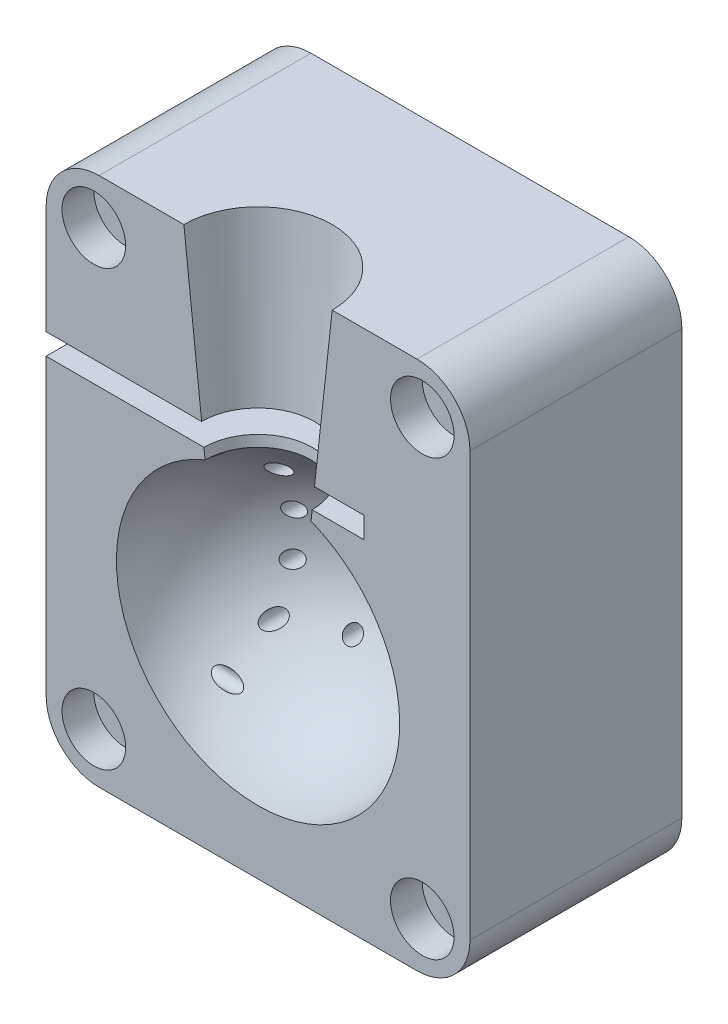
SolidWorks part; units mm, degrees
ref_plane "Alzado" through (0, 0, 0) normal (0, 0, 1) x (1, 0, 0)
ref_plane "Planta" through (0, 0, 0) normal (0, 1, 0) x (1, 0, 0)
ref_plane "Vista lateral" through (0, 0, 0) normal (1, 0, 0) x (0, 0, -1)
sketch "Sketch1" plane through (0, 0, 0) normal (0, 0, 1) x (1, 0, 0)
  line L0 (0, 0) -> (0, 50)
  line L1 (0, 50) -> (-40, 50)
  line L2 (-40, 50) -> (-40, 0)
  line L3 (-40, 0) -> (0, 0)
  dimension "D1" = 40
  dimension "D2" = 50
extrude "Boss-Extrude1" add sketch "Sketch1" against normal blind 20
sketch "Sketch2" plane through (0, 0, 0) normal (0, 0, 1) x (1, 0, 0)
  line L0 (-40, 50) -> (0, 50) construction
  line L1 (-20, 50) -> (-20, 0) construction
  line L2 (-40, 0) -> (0, 0) construction
  line L3 (-20, 32.73) -> (-20, 6)
  arc A0 (-20, 32.73) -> (-20, 6) centre (-20, 19.365) ccw
  dimension "D1" = 26.73
  dimension "D2" = 6
revolve "Cut-Revolve4" cut sketch "Sketch2" angle 360 about L1
sketch "Sketch3" plane through (0, 0, 0) normal (0, 0, 1) x (1, 0, 0)
  line L0 (-40, 50) -> (0, 50) construction
  line L1 (-20, -8.8718) -> (-20, 57.4274) construction
  line L2 (-27, 50) -> (-25, 31.7595)
  line L3 (-27, 50) -> (-20, 50)
  line L4 (-20, 50) -> (-20, 32.73)
  line L5 (-25, 31.7595) -> (-20, 32.73)
  circle A0 centre (-20, 19.365) radius 13.365 construction
  arc A1 (-25, 31.7595) -> (-20, 32.73) centre (-20, 19.365) cw
  dimension "D1" = 7
  dimension "D2" = 5
revolve "Cut-Revolve5" cut sketch "Sketch3" angle 360 about L1
ref_plane "Plane1" through (-20, 0, 0) normal (1, 0, 0) x (0, 0, -1)
sketch "Sketch6" plane through (0, 0, 0) normal (0, 0, 1) x (1, 0, 0)
  line L0 (-40.4401, 40.1066) -> (-40, 50) construction
  line L1 (-40, 50) -> (0, 50) construction
  line L2 (0, 50) -> (0, 0) construction
  line L3 (-20, 44.829) -> (-20, -4.3211) construction
  line L4 (-20, -11) -> (-20, 11) construction
  line L5 (-40, 25) -> (0, 25) construction
  line L6 (-40, 50) -> (-40, 0) construction
  circle A0 centre (-4.5, 45.5) radius 3
  circle A1 centre (-35.5, 45.5) radius 3
  circle A2 centre (-4.5, 4.5) radius 3
  circle A3 centre (-35.5, 4.5) radius 3
  dimension "D1" = 4.5
  dimension "D2" = 4.5
extrude "Cut-Extrude2" cut sketch "Sketch6" against normal blind 3
fillet "Fillet3" radius 5 4 edges at (-40, 0, -10) (0, 0, -10) (0, 50, -10) (-40, 50, -10)
sketch "Sketch10" plane through (0, 0, 0) normal (0, 0, 1) x (1, 0, 0)
  line L0 (-10, 34.735) -> (-10, 32.735)
  line L1 (-40, 32.735) -> (-10, 32.735)
  line L2 (-40, 45) -> (-40, 5) construction
  line L4 (-10, 34.735) -> (-40, 34.735)
  line L5 (-40, 34.735) -> (-40, 32.735)
  circle A1 centre (-20, 19.365) radius 13.37 construction
  arc A2 (-25, 31.7595) -> (-15, 31.7595) centre (-20, 19.365) ccw construction
  dimension "D1" = 26.74
  dimension "D2" = 30
  dimension "D3" = 2
extrude "Cut-Extrude5" cut sketch "Sketch10" against normal blind 10
sketch "Sketch13" plane through (0, 0, 0) normal (0, -1, 0) x (1, 0, 0)
  line L0 (-20, -14.5) -> (-6.5, -14.5)
  line L4 (-33.5, -14.5) -> (-20, -14.5)
  line L5 (-33.5, -16.5) -> (-30, -16.5)
  line L6 (-10, -16.5) -> (-6.5, -16.5)
  line L7 (-33.5, -20) -> (-6.5, -20)
  line L8 (-35, -20) -> (-5, -20) construction
  line L9 (-33.5, -20) -> (-30, -16.5)
  line L11 (-10, -16.5) -> (-6.5, -20)
  line L12 (-6.5, -16.5) -> (-6.5, -14.5)
  line L13 (-33.5, -14.5) -> (-33.5, -16.5)
  dimension "D4" = 5.5
  dimension "D5" = 45
  dimension "D6" = 45
extrude "Cut-Extrude7" cut sketch "Sketch13" against normal blind 30
sketch "Sketch14" plane through (0, 0, -14.5) normal (0, 0, -1) x (-1, 0, 0)
  line L0 (20, 31.7595) -> (20, -3.6539) construction
  line L1 (25, 31.7595) -> (15, 31.7595) construction
  line L2 (35, 0) -> (5, 0) construction
  circle A0 centre (27.5, 25) radius 0.75
  circle A1 centre (22.5, 25) radius 0.75
  circle A2 centre (27.5, 21) radius 0.75
  circle A3 centre (22.5, 21) radius 0.75
  circle A4 centre (27.5, 17) radius 0.75
  circle A5 centre (22.5, 17) radius 0.75
  circle A6 centre (27.5, 13) radius 0.75
  circle A7 centre (22.5, 13) radius 0.75
  circle A8 centre (17.5, 13) radius 0.75
  circle A9 centre (12.5, 13) radius 0.75
  circle A10 centre (17.5, 17) radius 0.75
  circle A11 centre (12.5, 17) radius 0.75
  circle A12 centre (17.5, 21) radius 0.75
  circle A13 centre (12.5, 21) radius 0.75
  circle A14 centre (17.5, 25) radius 0.75
  circle A15 centre (12.5, 25) radius 0.75
  dimension "D1" = 1.5
  dimension "D2" = 7.5
  dimension "D3" = 25
  dimension "D4" = 2
  dimension "D5" = 4
extrude "Cut-Extrude8" cut sketch "Sketch14" against normal up to surface (5.6226 mm away)
sketch "Sketch15" plane through (-40, 0, 0) normal (-1, 0, 0) x (0, 0, 1)
  line L0 (-20, 5) -> (0, 5) construction
  line L1 (0, 32.735) -> (0, 5) construction
  circle A0 centre (-5, 9.87) radius 0.75
  circle A1 centre (-5, 27.87) radius 0.75
  dimension "D1" = 1.5
  dimension "D2" = 1.5
  dimension "D3" = 18
  dimension "D4" = 4.87
  dimension "D5" = 5
  dimension "D6" = 5
extrude "Cut-Extrude9" cut sketch "Sketch15" against normal up to surface (13.0241 mm away)
sketch "Sketch16" plane through (-40, 0, 0) normal (-1, 0, 0) x (0, 0, 1)
  line L0 (-17.5, 27.87) -> (-7.5, 27.87) construction
  line L1 (0, 32.735) -> (0, 5) construction
  line L2 (-19.5, 9.87) -> (-7.5, 9.87) construction
  circle A0 centre (-5, 27.87) radius 0.75 construction
  circle A2 centre (-5, 9.87) radius 0.75 construction
  text T0 "CaCL2" font "Century Gothic" height in points 8
  text T1 "Alginate" font "Century Gothic" height in points 8
  dimension "D1" = 0
  dimension "D2" = 10
  dimension "D3" = 7.5
  dimension "D4" = 0
  dimension "D5" = 12
  dimension "D6" = 7.5
extrude "Cut-Extrude10" cut sketch "Sketch16" against normal blind 1
sketch "Sketch17" plane through (-40, 0, 0) normal (-1, 0, 0) x (0, 0, 1)
  circle A0 centre (-5, 27.87) radius 2.5
  circle A1 centre (-5, 9.87) radius 2.5
  dimension "D1" = 5
  dimension "D2" = 5
extrude "Cut-Extrude11" cut sketch "Sketch17" against normal blind 4
ref_plane "Plane2" through (0, 0, -5) normal (0, 0, 1) x (1, 0, 0)
sketch "Sketch19" plane through (0, 0, -5) normal (0, 0, 1) x (1, 0, 0)
  line L0 (-36, 28.62) -> (-40, 28.62)
  line L1 (-28.2443, 28.62) -> (-36, 28.62) construction
  line L2 (-40, 28.62) -> (-40, 28.87)
  line L3 (-40, 28.87) -> (-37.5, 29.42)
  line L4 (-37.5, 29.42) -> (-37.5, 29.17)
  line L5 (-37.5, 29.17) -> (-36, 29.17)
  line L6 (-36, 29.17) -> (-36, 28.62)
  line L10 (-36, 30.37) -> (-36, 25.37) construction
  line L11 (-36, 27.87) -> (-40.753, 27.87) construction
  line L12 (-36, 18.87) -> (-36, 28.62) construction
  dimension "D1" = 4
  dimension "D3" = 1.5
  dimension "D4" = 1
  dimension "D5" = 1.3
  dimension "D6" = 1.55
revolve "Revolve2" add sketch "Sketch19" angle 360 about L11
ref_plane "Plane3" through (0, 18.87, 0) normal (0, -1, 0) x (-1, 0, 0)
mirror "Mirror1" about plane through (0, 18.87, 0) normal (0, -1, 0) of "Revolve2"
